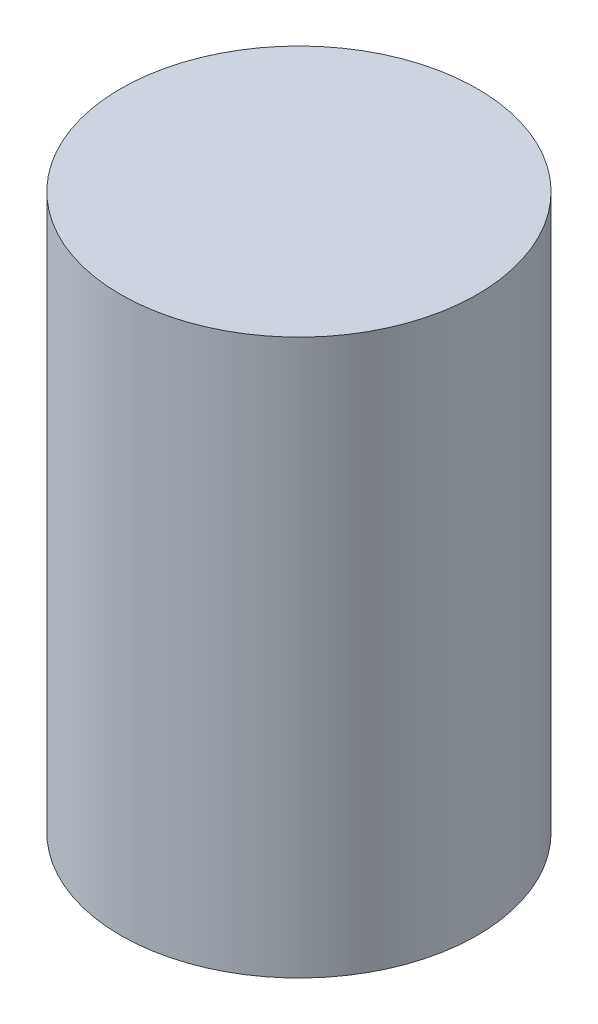
SolidWorks part; units mm, degrees
ref_plane "Front Plane" through (0, 0, 0) normal (0, 0, 1) x (1, 0, 0)
ref_plane "Top Plane" through (0, 0, 0) normal (0, 1, 0) x (1, 0, 0)
ref_plane "Right Plane" through (0, 0, 0) normal (1, 0, 0) x (0, 0, -1)
sketch "Base" plane through (0, 0, 0) normal (0, 1, 0) x (1, 0, 0)
  circle A0 centre (0, 0) radius 6.425
  dimension "D1" = 12.85
extrude "Boss-Extrude1" add sketch "Base" along normal blind 20
equation "\"Core_Diameter\"= \"Bore@Coil.Assembly\""
equation "\"D1@Base\" = \"Core_Diameter\""
equation "\"Core_Height\"= \"Coil_Height@Coil.Assembly\""
equation "\"D1@Boss-Extrude1\"=\"Core_Height\""
